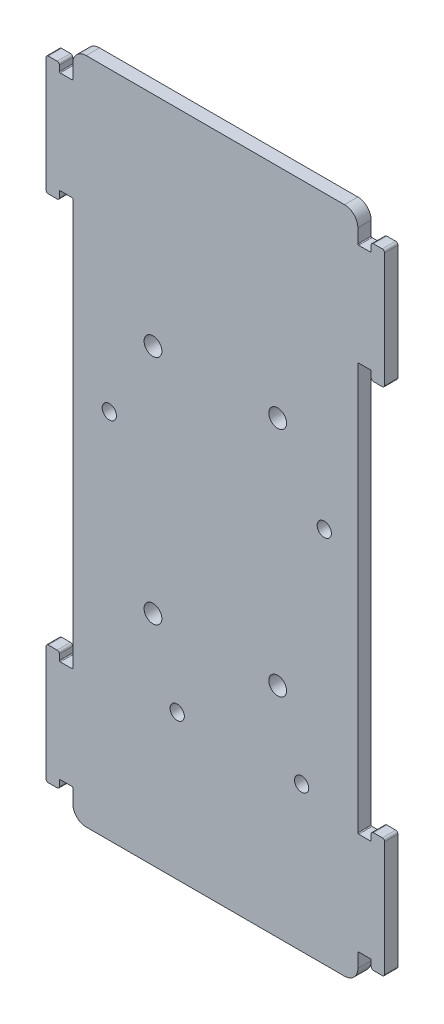
SolidWorks part; units mm, degrees
ref_plane "前视基准面" through (0, 0, 0) normal (0, 0, 1) x (1, 0, 0)
ref_plane "上视基准面" through (0, 0, 0) normal (0, 1, 0) x (1, 0, 0)
ref_plane "右视基准面" through (0, 0, 0) normal (1, 0, 0) x (0, 0, -1)
sketch "草图1" plane through (0, 0, 0) normal (0, 0, 1) x (1, 0, 0)
  line L0 (32.2, 68.7) -> (34.8, 68.7)
  line L1 (-29, 75) -> (29, 75)
  line L2 (-32, 72) -> (-32, -72) construction
  line L3 (-29, -75) -> (29, -75)
  line L4 (32, 72) -> (32, -72) construction
  line L5 (-32, 75) -> (32, -75) construction
  line L6 (-32, -75) -> (32, 75) construction
  line L7 (35, 68.9) -> (35, 70.15)
  line L8 (35.5, 70.65) -> (37.5, 70.65)
  line L9 (38, 70.15) -> (38, 44.35)
  line L10 (37.5, 43.85) -> (35.5, 43.85)
  line L11 (35, 44.35) -> (35, 45.6)
  line L12 (34.8, 45.8) -> (32.2, 45.8)
  line L13 (38, 57.25) -> (32, 57.25) construction
  line L14 (32, 68.9) -> (32, 72)
  line L15 (32, 45.6) -> (32, -45.6)
  line L16 (0, 0) -> (19.5271, 0) construction
  line L17 (0, 0) -> (0, 19.9471) construction
  line L18 (34.8, -45.8) -> (32.2, -45.8)
  line L19 (35, -44.35) -> (35, -45.6)
  line L20 (37.5, -43.85) -> (35.5, -43.85)
  line L21 (32, -68.9) -> (32, -72)
  line L22 (32.2, -68.7) -> (34.8, -68.7)
  line L23 (35, -68.9) -> (35, -70.15)
  line L24 (35.5, -70.65) -> (37.5, -70.65)
  line L25 (38, -70.15) -> (38, -44.35)
  line L26 (-37.5, 43.85) -> (-35.5, 43.85)
  line L27 (-35, 44.35) -> (-35, 45.6)
  line L28 (-34.8, 45.8) -> (-32.2, 45.8)
  line L29 (-32, 45.6) -> (-32, -45.6)
  line L30 (-34.8, -45.8) -> (-32.2, -45.8)
  line L31 (-35, -44.35) -> (-35, -45.6)
  line L32 (-37.5, -43.85) -> (-35.5, -43.85)
  line L33 (-38, -70.15) -> (-38, -44.35)
  line L34 (-35.5, -70.65) -> (-37.5, -70.65)
  line L35 (-35, -68.9) -> (-35, -70.15)
  line L36 (-32.2, -68.7) -> (-34.8, -68.7)
  line L37 (-32, -68.9) -> (-32, -72)
  line L38 (-37.5, 43.85) -> (-35.5, 43.85)
  line L39 (-32, 68.9) -> (-32, 72)
  line L40 (-32.2, 68.7) -> (-34.8, 68.7)
  line L41 (-35, 68.9) -> (-35, 70.15)
  line L42 (-35.5, 70.65) -> (-37.5, 70.65)
  line L43 (-38, 70.15) -> (-38, 44.35)
  arc A0 (-32, -72) -> (-29, -75) centre (-29, -72) ccw
  arc A1 (29, -75) -> (32, -72) centre (29, -72) ccw
  arc A2 (29, 75) -> (32, 72) centre (29, 72) cw
  arc A3 (-32, 72) -> (-29, 75) centre (-29, 72) cw
  arc A4 (35, 70.15) -> (35.5, 70.65) centre (35.5, 70.15) cw
  arc A5 (35, 44.35) -> (35.5, 43.85) centre (35.5, 44.35) ccw
  arc A6 (37.5, 43.85) -> (38, 44.35) centre (37.5, 44.35) ccw
  arc A7 (37.5, 70.65) -> (38, 70.15) centre (37.5, 70.15) cw
  arc A8 (37.5, 43.85) -> (38, 44.35) centre (37.5, 44.35) ccw
  arc A9 (34.8, 45.8) -> (35, 45.6) centre (34.8, 45.6) cw
  arc A10 (34.8, 68.7) -> (35, 68.9) centre (34.8, 68.9) ccw
  arc A11 (32, 45.6) -> (32.2, 45.8) centre (32.2, 45.6) cw
  arc A12 (32, 68.9) -> (32.2, 68.7) centre (32.2, 68.9) ccw
  arc A13 (32, -45.6) -> (32.2, -45.8) centre (32.2, -45.6) ccw
  arc A14 (34.8, -45.8) -> (35, -45.6) centre (34.8, -45.6) ccw
  arc A15 (35, -44.35) -> (35.5, -43.85) centre (35.5, -44.35) cw
  arc A16 (32, -68.9) -> (32.2, -68.7) centre (32.2, -68.9) cw
  arc A17 (34.8, -68.7) -> (35, -68.9) centre (34.8, -68.9) cw
  arc A18 (35, -70.15) -> (35.5, -70.65) centre (35.5, -70.15) ccw
  arc A19 (37.5, -70.65) -> (38, -70.15) centre (37.5, -70.15) ccw
  arc A20 (37.5, -43.85) -> (38, -44.35) centre (37.5, -44.35) cw
  arc A21 (-35, 44.35) -> (-35.5, 43.85) centre (-35.5, 44.35) cw
  arc A22 (-34.8, 45.8) -> (-35, 45.6) centre (-34.8, 45.6) ccw
  arc A23 (-32, 45.6) -> (-32.2, 45.8) centre (-32.2, 45.6) ccw
  arc A24 (-32, -45.6) -> (-32.2, -45.8) centre (-32.2, -45.6) cw
  arc A25 (-34.8, -45.8) -> (-35, -45.6) centre (-34.8, -45.6) cw
  arc A26 (-35, -44.35) -> (-35.5, -43.85) centre (-35.5, -44.35) ccw
  arc A27 (-37.5, -43.85) -> (-38, -44.35) centre (-37.5, -44.35) ccw
  arc A28 (-37.5, -70.65) -> (-38, -70.15) centre (-37.5, -70.15) cw
  arc A29 (-35, -70.15) -> (-35.5, -70.65) centre (-35.5, -70.15) cw
  arc A30 (-34.8, -68.7) -> (-35, -68.9) centre (-34.8, -68.9) ccw
  arc A31 (-32, -68.9) -> (-32.2, -68.7) centre (-32.2, -68.9) ccw
  arc A32 (-37.5, 43.85) -> (-38, 44.35) centre (-37.5, 44.35) cw
  arc A33 (-32, 68.9) -> (-32.2, 68.7) centre (-32.2, 68.9) cw
  arc A34 (-34.8, 68.7) -> (-35, 68.9) centre (-34.8, 68.9) cw
  arc A35 (-35, 70.15) -> (-35.5, 70.65) centre (-35.5, 70.15) ccw
  arc A36 (-37.5, 70.65) -> (-38, 70.15) centre (-37.5, 70.15) ccw
  point P0 (0, 0)
  point P33 (35, 69.525)
  point P45 (32, 45.8)
  point P53 (32, 68.7)
  point P75 (32, 0)
  point P77 (38, -57.25)
  dimension "D3" = 3
  dimension "D6" = 0.2
  dimension "D7" = 0.5
  dimension "D8" = 0.2
  dimension "D11" = 0.2
  dimension "D1" = 64
  dimension "D2" = 150
  dimension "D4" = 22.9
  dimension "D5" = 26.8
  dimension "D9" = 3
  dimension "D10" = 3
  dimension "D12" = 114.5
extrude "凸台-拉伸1" add sketch "草图1" along normal mid plane 3 contours L42 A36 L43 A32 L26 A21 L27 A22 L28 A23 L29 A24 L30 A25 L31 A26 L32 A27 L33 A28 L34 A29 L35 A30 L36 A31 L37 A0 L3 A1 L21 A16 L22 A17 L23 A18 L24 A19 L25 A20 L20 A15 L19 A14 L18 A13 L15 A11 L12 A9 L11
sketch "草图2" plane through (0, 0, -1.5) normal (0, 0, -1) x (-1, 0, 0)
  circle A0 centre (23.8, 8.34) radius 1.6
  circle A1 centre (8.56, -42.46) radius 1.6
  circle A2 centre (-19.38, -42.46) radius 1.6
  circle A3 centre (-24.46, 9.61) radius 1.6
  dimension "D1" = 3.2
  dimension "D2" = 3.2
  dimension "D3" = 3.2
  dimension "D4" = 3.2
extrude "切除-拉伸1" cut sketch "草图2" against normal up to next
sketch "草图3" plane through (0, 0, 1.5) normal (0, 0, 1) x (1, 0, 0)
  line L0 (0, 0) -> (11.2992, 0) construction
  line L1 (-14, 26) -> (14, 26) construction
  line L2 (-14, 26) -> (-14, -26) construction
  line L3 (-14, -26) -> (14, -26) construction
  line L4 (14, 26) -> (14, -26) construction
  line L5 (-14, 26) -> (14, -26) construction
  line L6 (-14, -26) -> (14, 26) construction
  line L7 (0, 0) -> (0, -11.627) construction
  circle A0 centre (14, 26) radius 2
  circle A1 centre (14, -26) radius 2
  circle A2 centre (-14, 26) radius 2
  circle A3 centre (-14, -26) radius 2
  point P0 (0, 0)
  dimension "D3" = 4
  dimension "D1" = 28
  dimension "D2" = 52
extrude "切除-拉伸2" cut sketch "草图3" against normal blind 10
